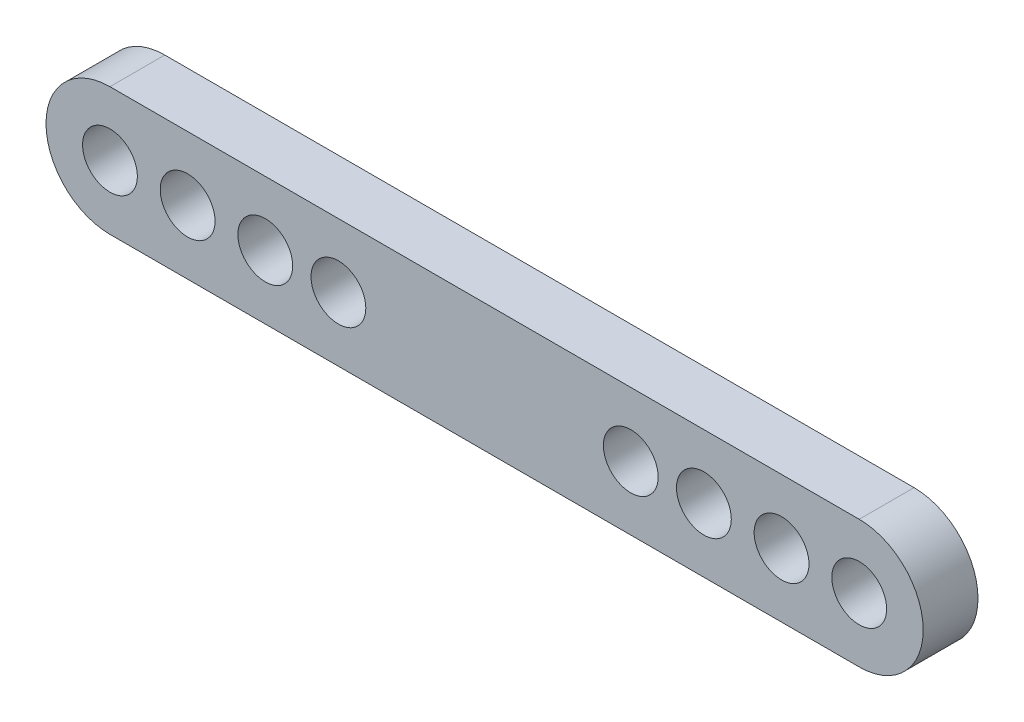
SolidWorks part; units mm, degrees
ref_plane "前视基准面" through (0, 0, 0) normal (0, 0, 1) x (1, 0, 0)
ref_plane "上视基准面" through (0, 0, 0) normal (0, 1, 0) x (1, 0, 0)
ref_plane "右视基准面" through (0, 0, 0) normal (1, 0, 0) x (0, 0, -1)
sketch "草图1" plane through (0, 0, 0) normal (0, 0, 1) x (1, 0, 0)
  line L0 (0, 8.3079) -> (0, 0) construction
  line L1 (0, 0) -> (0, -6.678) construction
  line L2 (-20.5, 3.5) -> (20.5, 3.5)
  line L3 (-20.5, -3.5) -> (20.5, -3.5)
  line L4 (-24, 0) -> (24, 0) construction
  circle A0 centre (-20.5, 0) radius 1.5
  arc A1 (-20.5, -3.5) -> (-20.5, 3.5) centre (-20.5, 0) cw
  arc A2 (20.5, -3.5) -> (20.5, 3.5) centre (20.5, 0) ccw
  circle A4 centre (-16.25, 0) radius 1.5
  circle A5 centre (-12, 0) radius 1.5
  circle A6 centre (-8, 0) radius 1.5
  circle A11 centre (8, 0) radius 1.5
  circle A12 centre (12, 0) radius 1.5
  circle A13 centre (16.25, 0) radius 1.5
  circle A14 centre (20.5, 0) radius 1.5
  point P11 (0, -3.5)
  point P12 (0, 3.5)
  point P21 (8, 0)
  point P22 (12, 0)
  point P23 (16.25, 0)
  dimension "D1" = 3
  dimension "D3" = 3.5
  dimension "D7" = 3
  dimension "D8" = 3
  dimension "D9" = 3
  dimension "D10" = 3
  dimension "D11" = 3
  dimension "D12" = 3
  dimension "D13" = 3
  dimension "D2" = 20.5
  dimension "D4" = 8
  dimension "D5" = 12
  dimension "D6" = 16.25
extrude "凸台-拉伸1" add sketch "草图1" along normal blind 3
